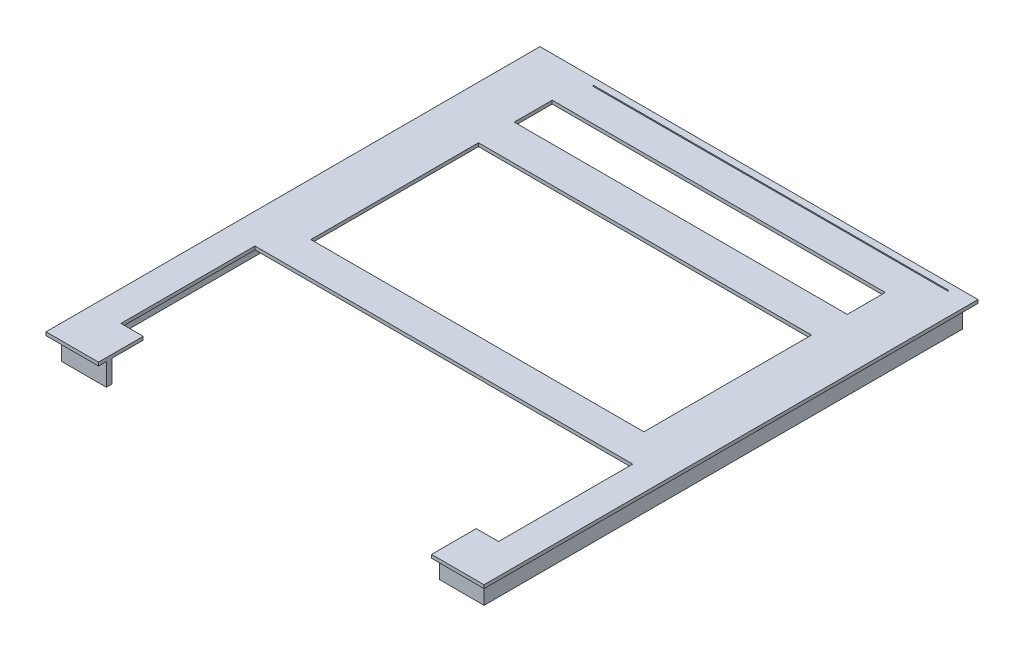
SolidWorks part; units mm, degrees
ref_plane "前视基准面" through (0, 0, 0) normal (0, 0, 1) x (1, 0, 0)
ref_plane "上视基准面" through (0, 0, 0) normal (0, 1, 0) x (1, 0, 0)
ref_plane "右视基准面" through (0, 0, 0) normal (1, 0, 0) x (0, 0, -1)
sketch "草图1" plane through (0, 0, 0) normal (0, 1, 0) x (1, 0, 0)
  line L0 (3.5, 217.5) -> (192.5, 217.5)
  line L1 (0, 0) -> (196, 0)
  line L2 (0, 0) -> (0, 221)
  line L3 (0, 221) -> (196, 221)
  line L4 (196, 0) -> (196, 221)
  line L5 (192.5, 3.5) -> (192.5, 217.5)
  line L6 (3.5, 3.5) -> (192.5, 3.5)
  line L7 (3.5, 3.5) -> (3.5, 217.5)
  dimension "D1" = 3.5
extrude "凸台-拉伸1" add sketch "草图1" along normal blind 1.5 contours L1 L4 L3 L2
sketch "草图2" plane through (0, 0, 0) normal (0, 1, 0) x (1, 0, 0)
  line L4 (196, 221) -> (186, 221)
  line L5 (0, 221) -> (196, 221) construction
  line L6 (0, 221) -> (27, 221)
  line L7 (27, 221) -> (27, 215)
  line L8 (3.5, 3.5) -> (192.5, 3.5)
  line L9 (192.5, 3.5) -> (192.5, 217.5)
  line L10 (3.5, 217.5) -> (3.5, 3.5)
  line L11 (192.5, 217.5) -> (3.5, 217.5)
  line L12 (3.5, 3.5) -> (192.5, 3.5)
  line L13 (192.5, 3.5) -> (192.5, 217.5)
  line L14 (3.5, 217.5) -> (3.5, 3.5)
  line L15 (192.5, 217.5) -> (3.5, 217.5)
  line L16 (27, 215) -> (6, 215)
  line L17 (6, 215) -> (6, 6)
  line L18 (0, 6) -> (23.5, 6)
  line L19 (0, 0) -> (0, 221) construction
  line L20 (23.5, 3.5) -> (3.5, 3.5)
  line L21 (3.5, 217.5) -> (27, 217.5)
  line L22 (27, 217.5) -> (27, 215)
  line L23 (186, 221) -> (186, 215)
  line L24 (186, 215) -> (190, 215)
  line L25 (190, 215) -> (190, 6)
  line L26 (196, 6) -> (172.5, 6)
  line L27 (196, 0) -> (196, 221) construction
  line L28 (172.5, 6) -> (172.5, 3.5)
  line L29 (172.5, 3.5) -> (192.5, 3.5)
  line L30 (192.5, 217.5) -> (186, 217.5)
  line L31 (27, 221) -> (186, 221)
  line L32 (27, 221) -> (27, 218)
  line L33 (27, 218) -> (186, 218)
  line L34 (186, 218) -> (186, 221)
  line L35 (27, 215) -> (27, 216.5)
  line L36 (27, 216.5) -> (186, 216.5)
  line L37 (186, 216.5) -> (186, 215)
  line L38 (186, 215) -> (27, 215)
  line L39 (23.5, 6) -> (23.5, 3.5)
  dimension "D1" = 3.5
ref_plane "基准面1" through (0, 0, 0) normal (0, 1, 0) x (1, 0, 0)
sketch "草图3" plane through (0, 0, 0) normal (0, 1, 0) x (1, 0, 0)
  line L0 (3.5, 217.5) -> (27, 217.5)
  line L1 (27, 217.5) -> (27, 216.5)
  line L2 (27, 216.5) -> (186, 216.5)
  line L3 (186, 216.5) -> (186, 217.5)
  line L4 (186, 217.5) -> (192.5, 217.5)
  line L5 (192.5, 217.5) -> (192.5, 6)
  line L6 (192.5, 3.5) -> (192.5, 217.5) construction
  line L7 (196, 6) -> (172.5, 6) construction
  line L8 (192.5, 6) -> (192.5, 3.5)
  line L9 (192.5, 3.5) -> (172.5, 3.5)
  line L10 (172.5, 3.5) -> (172.5, 6)
  line L11 (172.5, 6) -> (190, 6)
  line L12 (190, 215) -> (6, 215)
  line L13 (6, 215) -> (6, 6)
  line L14 (6, 6) -> (23.5, 6)
  line L15 (23.5, 6) -> (23.5, 3.5)
  line L16 (23.5, 3.5) -> (3.5, 3.5)
  line L17 (3.5, 3.5) -> (3.5, 217.5)
  line L18 (190, 215) -> (190, 6)
extrude "凸台-拉伸2" add sketch "草图3" against normal blind 10 and the other way blind 1.5
sketch "草图4" plane through (0, 0, 0) normal (0, 1, 0) x (1, 0, 0)
  line L0 (27, 221) -> (186, 221)
  line L1 (186, 221) -> (186, 218)
  line L2 (186, 218) -> (27, 218)
  line L3 (27, 218) -> (27, 221)
extrude "凸台-拉伸3" add sketch "草图4" against normal blind 1.5
sketch "草图5" plane through (0, 0, 0) normal (0, 1, 0) x (1, 0, 0)
  line L0 (23.5, 3.5) -> (23.5, 0)
  line L1 (0, 0) -> (196, 0) construction
  line L2 (23.5, 0) -> (23.5, 3.5)
  line L3 (23.5, 3.5) -> (172.5, 3.5)
  line L4 (172.5, 3.5) -> (172.5, 0)
  line L5 (172.5, 0) -> (23.5, 0)
sketch "草图6" plane through (0, 0, 0) normal (0, 1, 0) x (1, 0, 0)
  line L1 (172.5, 3.5) -> (172.5, 0)
  line L3 (23.5, 0) -> (23.5, 3.5)
ref_plane "基准面2" through (0, 1.5, 0) normal (0, 1, 0) x (1, 0, 0)
sketch "草图8" plane through (0, 1.5, 0) normal (0, 1, 0) x (1, 0, 0)
  line L0 (23.5, 0) -> (172.5, 0)
  line L1 (27, 217.5) -> (27, 218)
  line L2 (172.5, 80) -> (23.5, 80)
  line L3 (172.5, 80) -> (182.5, 80)
  line L4 (27, 218) -> (186, 218)
  line L5 (23.5, 170) -> (23.5, 95)
  line L6 (172.5, 170) -> (23.5, 170)
  line L7 (23.5, 95) -> (172.5, 95)
  line L8 (172.5, 95) -> (172.5, 170)
  line L9 (23.5, 80) -> (13.5, 80)
  line L10 (23.5, 203) -> (172.5, 203)
  line L11 (172.5, 203) -> (172.5, 186)
  line L12 (172.5, 186) -> (23.5, 186)
  line L13 (23.5, 186) -> (23.5, 203)
  line L14 (13.5, 80) -> (13.5, 20)
  line L15 (13.5, 20) -> (23.5, 20)
  line L16 (23.5, 20) -> (23.5, 0)
  line L17 (182.5, 80) -> (182.5, 20)
  line L18 (182.5, 20) -> (172.5, 20)
  line L19 (172.5, 20) -> (172.5, 0)
  line L20 (186, 218) -> (186, 217.5)
  line L21 (186, 217.5) -> (27, 217.5)
extrude "切除-拉伸5" cut sketch "草图8" against normal blind 41.5
